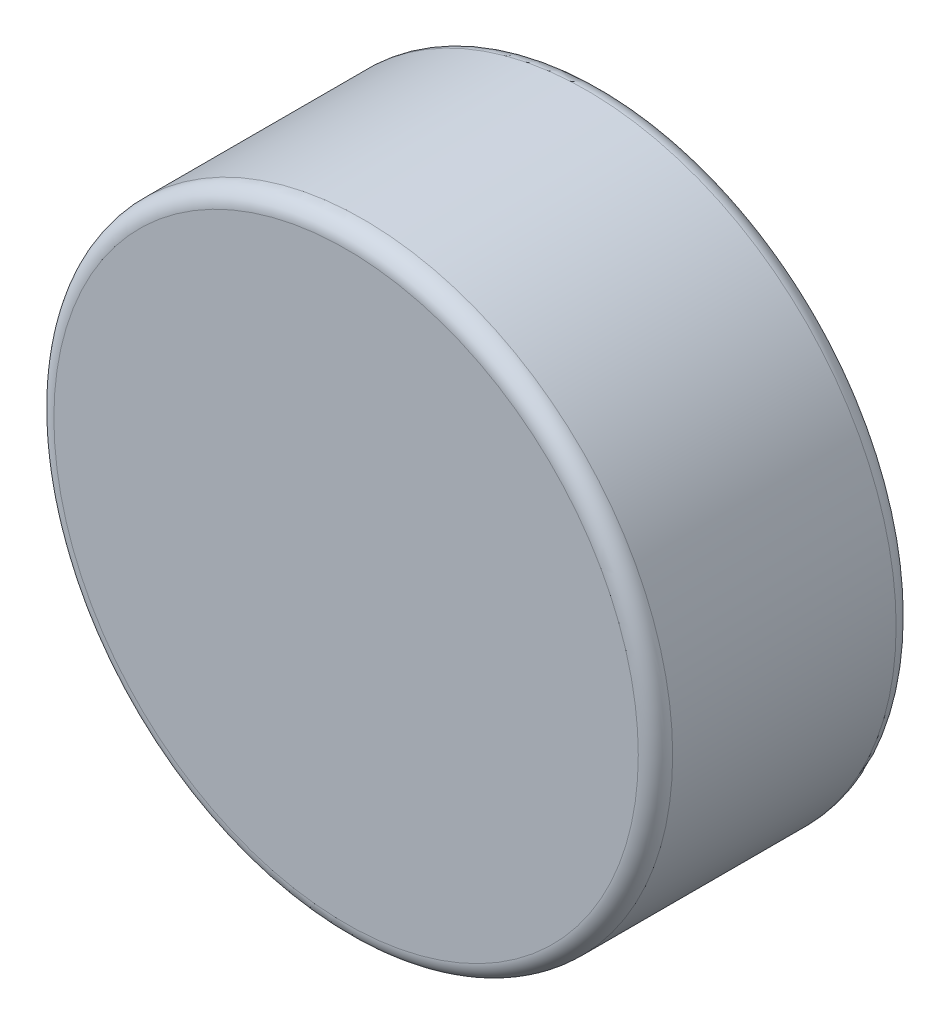
SolidWorks part; units mm, degrees
ref_plane "前视基准面" through (0, 0, 0) normal (0, 0, 1) x (1, 0, 0)
ref_plane "上视基准面" through (0, 0, 0) normal (0, 1, 0) x (1, 0, 0)
ref_plane "右视基准面" through (0, 0, 0) normal (1, 0, 0) x (0, 0, -1)
sketch "草图1" plane through (0, 0, 0) normal (0, 0, 1) x (1, 0, 0)
  circle A0 centre (0, 0) radius 3.6
  dimension "D1" = 7.2
extrude "凸台-拉伸1" add sketch "草图1" along normal blind 3
fillet "圆角1" radius 0.2 2 edges at (3.6, 0, 0) (3.6, 0, 3)
